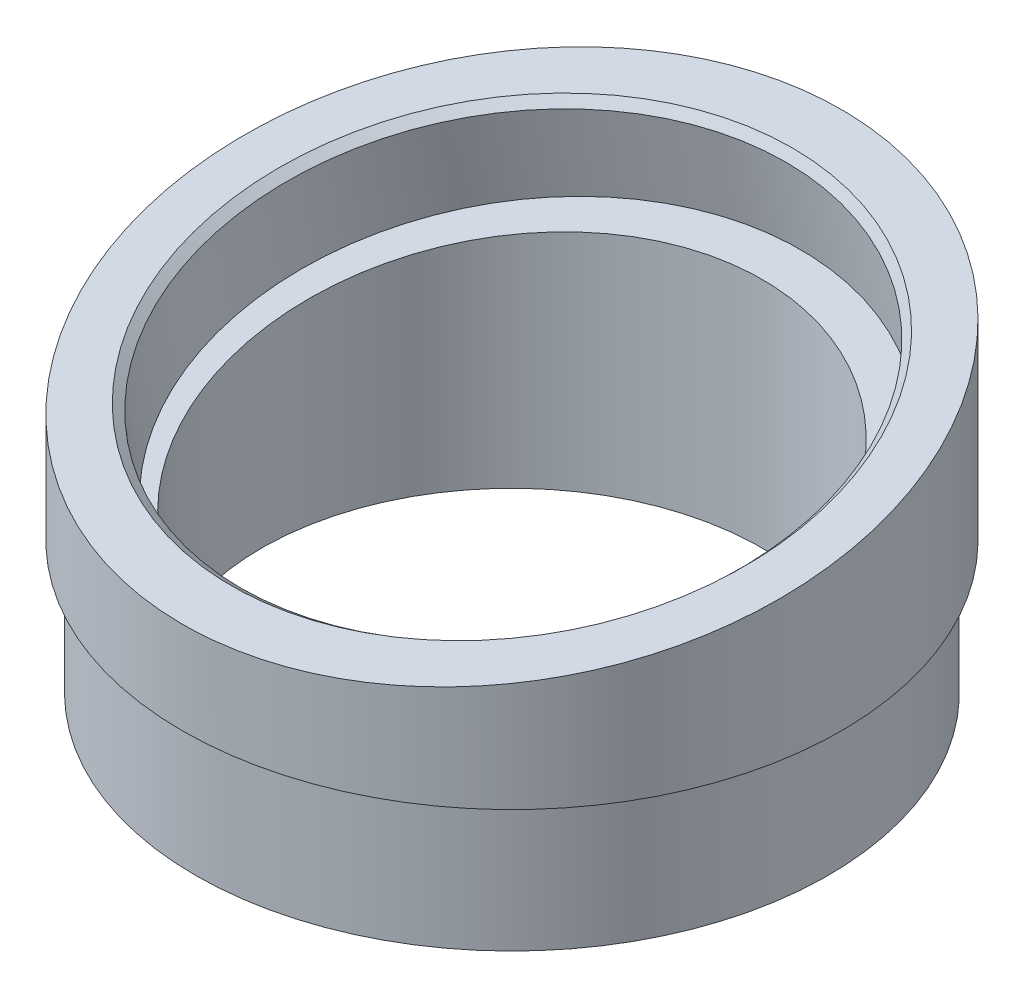
SolidWorks part; units mm, degrees
material "ABS"
ref_plane "前视基准面" through (0, 0, 0) normal (0, 0, 1) x (1, 0, 0)
ref_plane "上视基准面" through (0, 0, 0) normal (0, 1, 0) x (1, 0, 0)
ref_plane "右视基准面" through (0, 0, 0) normal (1, 0, 0) x (0, 0, -1)
sketch "草图1" plane through (0, 0, 0) normal (0, 1, 0) x (1, 0, 0)
  circle A0 centre (0, 0) radius 24
  circle A1 centre (0, 0) radius 19
  dimension "D1" = 48
  dimension "D2" = 38
extrude "凸台-拉伸1" add sketch "草图1" along normal blind 10
sketch "草图2" plane through (0, 10, 0) normal (0, 1, 0) x (1, 0, 0)
  circle A0 centre (0, 0) radius 25
  circle A1 centre (0, 0) radius 19
  dimension "D1" = 50
  dimension "D2" = 38
extrude "凸台-拉伸2" add sketch "草图2" along normal blind 20
sketch "草图3" plane through (0, 0, 0) normal (1, 0, 0) x (0, 0, -1)
  line L0 (-25, 17) -> (25, 25.8163)
  line L1 (-25, 30) -> (-25, 10) construction
  line L2 (25, 10) -> (25, 30) construction
  line L3 (-24, 10) -> (24, 10) construction
  line L4 (25, 25.8163) -> (25, 47.8795)
  line L5 (25, 47.8795) -> (-25, 47.8795)
  line L6 (-25, 47.8795) -> (-25, 17)
  dimension "D1" = 7
  dimension "D2" = 10
extrude "切除-拉伸1" cut sketch "草图3" against normal mid plane 62
sketch "草图4" plane through (0, 20.7626, 3.661) normal (0, 0.9848, 0.1736) x (1, 0, 0)
  circle A0 centre (0, 3.7175) radius 21
  dimension "D1" = 42
extrude "切除-拉伸2" cut sketch "草图4" against normal blind 7
chamfer "倒角1" distance 0.6 angle 45 1 edges at (0, 17.7616, 20.681)
